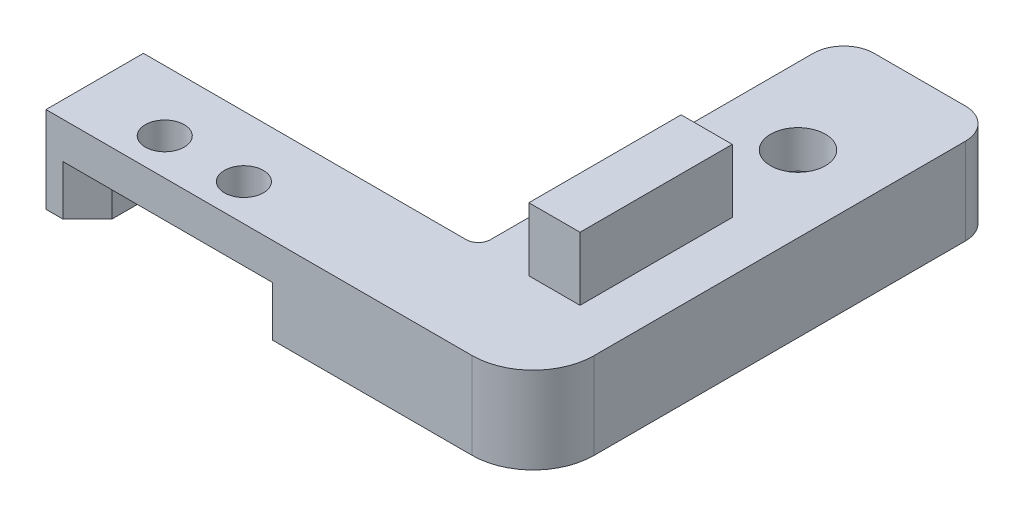
SolidWorks part; units mm, degrees
material "ABS PC"
ref_plane "Front Plane" through (0, 0, 0) normal (0, 0, 1) x (1, 0, 0)
ref_plane "Top Plane" through (0, 0, 0) normal (0, 1, 0) x (1, 0, 0)
ref_plane "Right Plane" through (0, 0, 0) normal (1, 0, 0) x (0, 0, -1)
sketch "Sketch1" plane through (0, 0, 0) normal (0, 1, 0) x (1, 0, 0)
  line L1 (0, 0) -> (-12.5, 0)
  line L2 (0, 0) -> (0, -38)
  line L3 (0, -38) -> (-12.5, -38)
  line L4 (-12.5, 0) -> (-12.5, -30)
  line L5 (-12.5, -38) -> (-40, -38)
  line L7 (-12.5, -30) -> (-40, -30)
  line L8 (-40, -38) -> (-40, -30)
  dimension "D1" = 12.5
  dimension "D2" = 40
  dimension "D3" = 8
  dimension "D4" = 30
extrude "Boss-Extrude1" add sketch "Sketch1" along normal blind 7.1
sketch "Sketch2" plane through (0, 7.1, 0) normal (0, 1, 0) x (1, 0, 0)
  line L0 (-6.25, 0) -> (-6.25, -8.1286) construction
  line L1 (-8.35, -17.5) -> (-4.15, -17.5)
  line L2 (-8.35, -17.5) -> (-8.35, -30)
  line L3 (-8.35, -30) -> (-4.15, -30)
  line L4 (-4.15, -17.5) -> (-4.15, -30)
  line L5 (0, 0) -> (-12.5, 0) construction
  line L6 (-12.5, -30) -> (-40, -30) construction
  point P8 (-6.25, -17.5)
  dimension "D1" = 4.2
  dimension "D3" = 17.5
extrude "Boss-Extrude2" add sketch "Sketch2" along normal blind 5.2
sketch "Sketch3" plane through (0, 0, 0) normal (0, -1, 0) x (1, 0, 0)
  line L0 (-6.25, 0) -> (-6.25, 14.9643) construction
  line L1 (0, 0) -> (-12.5, 0) construction
  point P4 (-6.25, 10)
  dimension "D1" = 10
hole_wizard "CBORE for M4 SHCS1" positions "Sketch3" profile "Sketch4" counterbore size "M4" standard "ANSI Metric" end condition through all
sketch "Sketch4" plane through (-6.25, 0, 10) normal (1, 0, 0) x (0, 0, -1)
  line L0 (0, 0) -> (0, 12.3)
  line L1 (0, 12.3) -> (2.25, 12.3)
  line L3 (2.25, 12.3) -> (2.25, 4)
  line L4 (2.25, 4) -> (4, 4)
  line L5 (4, 4) -> (4, 0)
  line L7 (4, 0) -> (0, 0)
  line L11 (0, -6.35) -> (0, 107.95) construction
  dimension "Thru Hole Dia." = 4.5
  dimension "Thru Hole Depth" = 12.3
  dimension "C'Bore Dia." = 8
  dimension "C'Bore Depth" = 4
sketch "Sketch5" plane through (0, 0, 0) normal (0, -1, 0) x (1, 0, 0)
  line L0 (-30, 30) -> (-30, 38) construction
  line L1 (-12.5, 30) -> (-40, 30) construction
  line L2 (-40, 38) -> (0, 38) construction
  line L3 (-22.6678, 35) -> (-37.3322, 35) construction
  line L4 (-40, 30) -> (-40, 38) construction
  point P9 (-30, 34)
  point P11 (-26.75, 35)
  point P12 (-33.25, 35)
  dimension "D1" = 10
  dimension "D2" = 6.5
  dimension "D3" = 5
hole_wizard "Ø3.2 (3.2) Diameter Hole1" positions "Sketch5" profile "Sketch6" hole size "Ø3.2" standard "ANSI Metric"
sketch "Sketch6" plane through (-33.25, 0, 35) normal (1, 0, 0) x (0, 0, -1)
  line L0 (0, 0) -> (0, 12.3)
  line L1 (0, 12.3) -> (1.6, 12.3)
  line L2 (1.6, 12.3) -> (1.6, 0)
  line L5 (1.6, 0) -> (0, 0)
  line L11 (0, -6.35) -> (0, 107.95) construction
  dimension "Thru Hole Dia." = 3.2
  dimension "Thru Hole Depth" = 12.3
sketch "Sketch7" plane through (0, 0, 0) normal (0, -1, 0) x (1, 0, 0)
  line L0 (-12.5, 30) -> (-40, 30) construction
  line L1 (-23.4, 30) -> (-36.6, 30)
  line L2 (-23.4, 30) -> (-23.4, 38)
  line L3 (-23.4, 38) -> (-36.6, 38)
  line L4 (-36.6, 30) -> (-36.6, 38)
  line L5 (-26.75, 35) -> (-33.25, 35) construction
  line L6 (-30, 38) -> (-30, 30) construction
  point P12 (-30, 35)
  dimension "D1" = 13.2
  dimension "D2" = 8
extrude "Cut-Extrude1" cut sketch "Sketch7" against normal blind 4.1
fillet "Fillet1" radius 5 1 edges at (0, 3.55, 38)
fillet "Fillet2" radius 2.5 2 edges at (-12.5, 3.55, 0) (0, 3.55, 0)
fillet "Fillet3" radius 1 1 edges at (-12.5, 3.55, 30)
chamfer "Chamfer1" distance 2 angle 45 2 edges at (-36.6, 2.05, 38) (-23.4, 2.05, 38)
